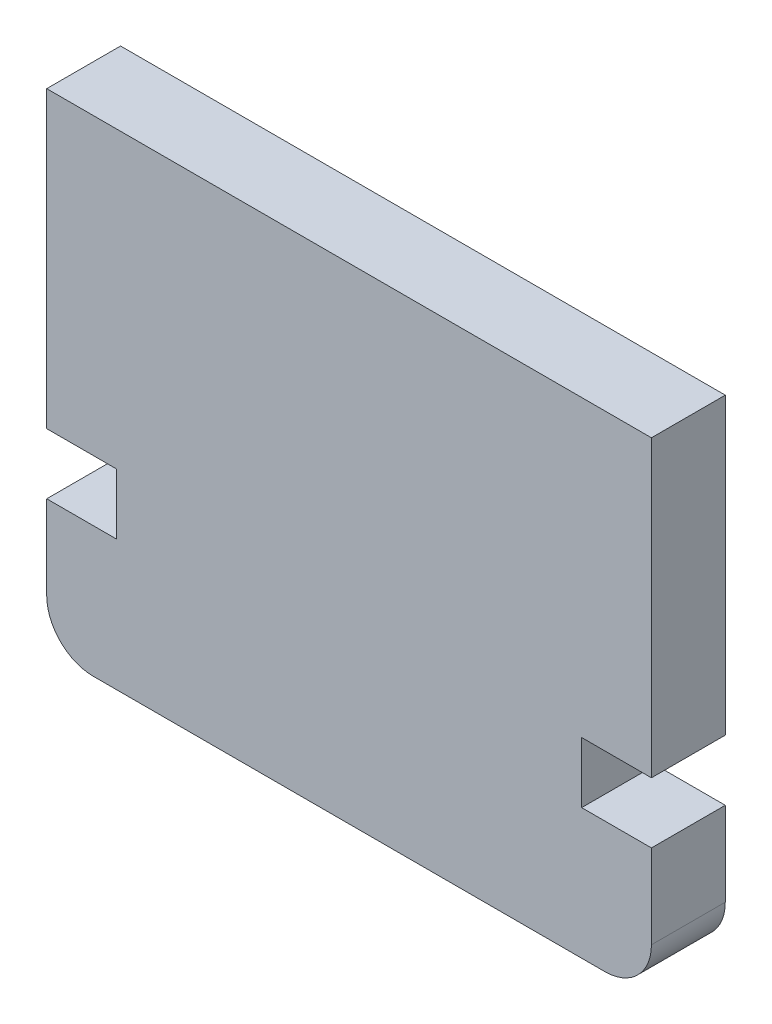
SolidWorks part; units mm, degrees
ref_plane "Front Plane" through (0, 0, 0) normal (0, 0, 1) x (1, 0, 0)
ref_plane "Top Plane" through (0, 0, 0) normal (0, 1, 0) x (1, 0, 0)
ref_plane "Right Plane" through (0, 0, 0) normal (1, 0, 0) x (0, 0, -1)
sketch "Sketch1" plane through (0, 0, 0) normal (0, 0, 1) x (1, 0, 0)
  line L0 (-27.95, 18.625) -> (-1.95, 18.625)
  line L3 (-25.95, -2.255) -> (-3.95, -2.255)
  line L5 (-27.95, 5.9637) -> (-24.95, 5.9637)
  line L6 (-24.95, 3.9116) -> (-24.95, 6.245) construction
  line L9 (-27.95, 18.625) -> (-27.95, 5.9637)
  line L10 (-27.95, 2.795) -> (-27.95, -0.255)
  line L11 (-1.95, 5.9637) -> (-4.95, 5.9637)
  line L12 (-4.95, 6.245) -> (-4.95, 3.9116) construction
  line L15 (-1.95, 18.625) -> (-1.95, 5.9637)
  line L16 (-1.95, 2.795) -> (-1.95, -0.255)
  line L17 (-24.95, 5.9637) -> (-24.95, 3.3533)
  line L18 (-24.95, 2.795) -> (-24.95, 3.9116) construction
  line L19 (-24.95, 3.3533) -> (-27.95, 3.3533)
  line L20 (-27.95, 2.795) -> (-27.95, 4.495) construction
  line L21 (-27.95, 3.3533) -> (-27.95, 2.795)
  line L22 (-4.95, 3.3533) -> (-1.95, 3.3533)
  line L23 (-1.95, 2.795) -> (-1.95, 4.495) construction
  line L24 (-1.95, 3.3533) -> (-1.95, 2.795)
  line L25 (-4.95, 5.9637) -> (-4.95, 3.3533)
  arc A0 (-3.95, -2.255) -> (-1.95, -0.255) centre (-3.95, -0.255) ccw
  arc A1 (-27.95, -0.255) -> (-25.95, -2.255) centre (-25.95, -0.255) ccw
extrude "Boss-Extrude1" add sketch "Sketch1" along normal blind 3.175
